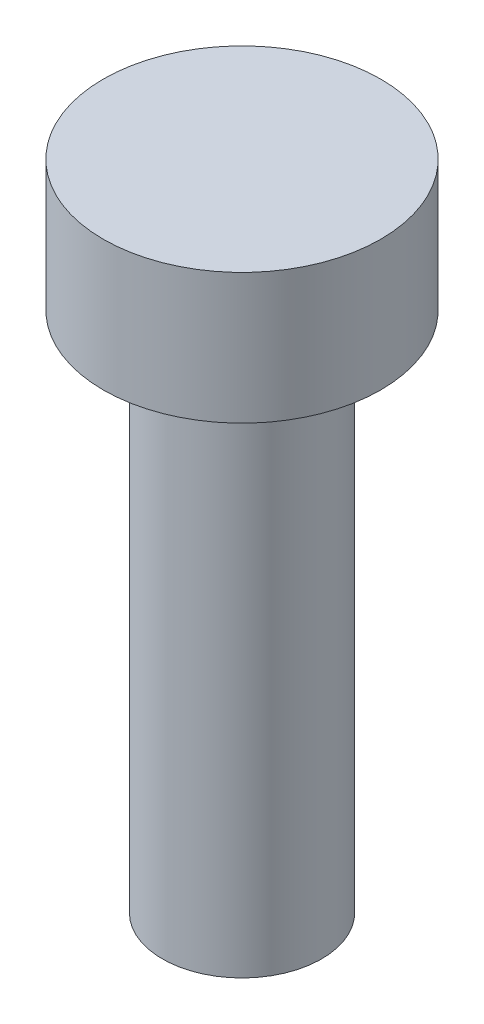
SolidWorks part; units mm, degrees
ref_plane "Front Plane" through (0, 0, 0) normal (0, 0, 1) x (1, 0, 0)
ref_plane "Top Plane" through (0, 0, 0) normal (0, 1, 0) x (1, 0, 0)
ref_plane "Right Plane" through (0, 0, 0) normal (1, 0, 0) x (0, 0, -1)
sketch "Sketch1" plane through (0, 0, 0) normal (0, 1, 0) x (1, 0, 0)
  circle A0 centre (0, 0) radius 4.25
  dimension "D1" = 8.5
extrude "Boss-Extrude1" add sketch "Sketch1" along normal blind 4
sketch "Sketch2" plane through (0, 0, 0) normal (0, -1, 0) x (1, 0, 0)
  circle A0 centre (0, 0) radius 2.44
  dimension "D1" = 4.88
extrude "Boss-Extrude2" add sketch "Sketch2" along normal blind 16
